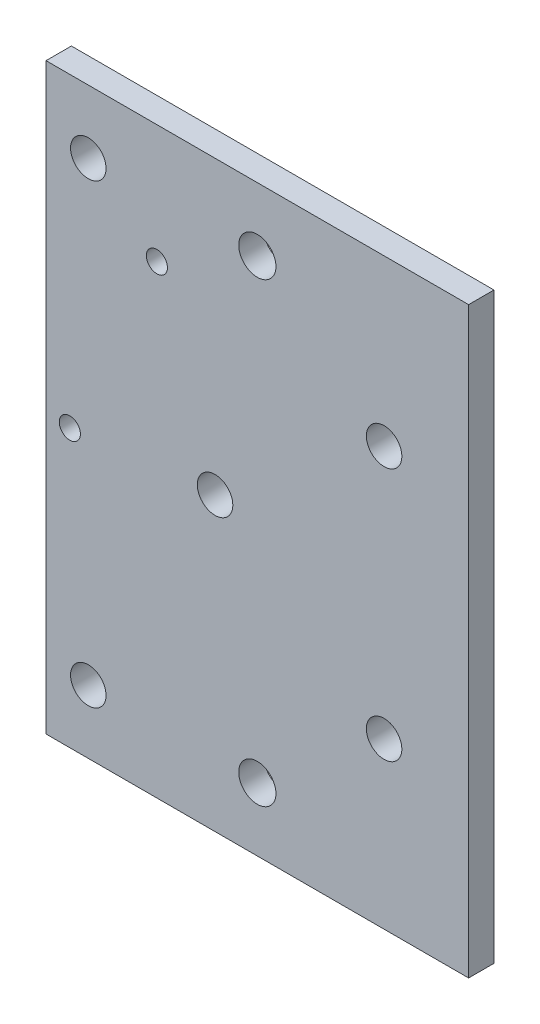
SolidWorks part; units mm, degrees
ref_plane "正面" through (0, 0, 0) normal (0, 0, 1) x (1, 0, 0)
ref_plane "平面" through (0, 0, 0) normal (0, 1, 0) x (1, 0, 0)
ref_plane "右側面" through (0, 0, 0) normal (1, 0, 0) x (0, 0, -1)
sketch "ｽｹｯﾁ1" plane through (0, 0, 0) normal (0, 0, 1) x (1, 0, 0)
  line L1 (-20, 14.5) -> (20, 14.5)
  line L2 (-20, 14.5) -> (-20, -14.5)
  line L3 (-20, -14.5) -> (20, -14.5)
  line L4 (20, 14.5) -> (20, -14.5)
  line L5 (-20, 14.5) -> (20, -14.5) construction
  line L6 (-20, -14.5) -> (20, 14.5) construction
  point P0 (0, 0)
  dimension "D1" = 29
  dimension "D2" = 40
extrude "ﾎﾞｽ - 押し出し1" add sketch "ｽｹｯﾁ1" along normal blind 3
sketch "ｽｹｯﾁ2" plane through (0, 0, 3) normal (0, 0, 1) x (1, 0, 0)
  line L1 (-20, 14.5) -> (-16.5, 14.5)
  line L2 (-20, 14.5) -> (-20, 10.5)
  line L3 (-20, 10.5) -> (-16.5, 10.5)
  line L4 (-16.5, 14.5) -> (-16.5, 10.5)
  line L5 (-20, -14.5) -> (-16.5, -14.5)
  line L6 (-20, -14.5) -> (-20, -10.5)
  line L7 (-20, -10.5) -> (-16.5, -10.5)
  line L8 (-16.5, -14.5) -> (-16.5, -10.5)
  line L9 (20, -14.5) -> (16.5, -14.5)
  line L10 (20, -14.5) -> (20, -10.5)
  line L11 (20, -10.5) -> (16.5, -10.5)
  line L12 (16.5, -14.5) -> (16.5, -10.5)
  line L13 (20, 14.5) -> (16.5, 14.5)
  line L14 (20, 14.5) -> (20, 10.5)
  line L15 (20, 10.5) -> (16.5, 10.5)
  line L16 (16.5, 14.5) -> (16.5, 10.5)
  circle A0 centre (-16.5, 10.5) radius 2.1
  circle A1 centre (-16.5, -10.5) radius 2.1
  circle A2 centre (16.5, -10.5) radius 2.1
  circle A3 centre (16.5, 10.5) radius 2.1
  dimension "D9" = 4.2
  dimension "D10" = 4.2
  dimension "D11" = 4.2
  dimension "D12" = 4.2
  dimension "D1" = 3.5
  dimension "D2" = 4
  dimension "D3" = 3.5
  dimension "D4" = 4
  dimension "D5" = 3.5
  dimension "D6" = 4
  dimension "D7" = 3.5
  dimension "D8" = 4
sketch "ｽｹｯﾁ3" plane through (0, -14.5, 0) normal (0, -1, 0) x (-1, 0, 0)
  line L0 (20, 0) -> (-20, 0) construction
  line L1 (20, -3) -> (-20, -3)
  line L2 (20, -3) -> (20, 0)
  line L3 (20, 0) -> (-20, 0)
  line L4 (-20, -3) -> (-20, 0)
extrude "ﾎﾞｽ - 押し出し2" add sketch "ｽｹｯﾁ3" along normal blind 3
sketch "ｽｹｯﾁ4" plane through (0, 14.5, 0) normal (0, 1, 0) x (1, 0, 0)
  line L1 (20, -3) -> (-20, -3)
  line L2 (20, -3) -> (20, 0)
  line L3 (20, 0) -> (-20, 0)
  line L4 (-20, -3) -> (-20, 0)
extrude "ﾎﾞｽ - 押し出し3" add sketch "ｽｹｯﾁ4" along normal blind 3
sketch "ｽｹｯﾁ5" plane through (0, -17.5, 0) normal (0, -1, 0) x (1, 0, 0)
  line L1 (20, 3) -> (-20, 3)
  line L2 (20, 3) -> (20, 0)
  line L3 (20, 0) -> (-20, 0)
  line L4 (-20, 3) -> (-20, 0)
extrude "ﾎﾞｽ - 押し出し4" add sketch "ｽｹｯﾁ5" along normal blind 7
sketch "ｽｹｯﾁ6" plane through (0, 17.5, 0) normal (0, 1, 0) x (1, 0, 0)
  line L1 (-20, -3) -> (20, -3)
  line L2 (-20, -3) -> (-20, 0)
  line L3 (-20, 0) -> (20, 0)
  line L4 (20, -3) -> (20, 0)
extrude "ﾎﾞｽ - 押し出し5" add sketch "ｽｹｯﾁ6" along normal blind 7
sketch "ｽｹｯﾁ7" plane through (0, 24.5, 0) normal (0, 1, 0) x (1, 0, 0)
  line L1 (-20, -3) -> (20, -3)
  line L2 (-20, -3) -> (-20, 0)
  line L3 (-20, 0) -> (20, 0)
  line L4 (20, -3) -> (20, 0)
extrude "ﾎﾞｽ - 押し出し6" add sketch "ｽｹｯﾁ7" along normal blind 10
sketch "ｽｹｯﾁ8" plane through (0, -24.5, 0) normal (0, -1, 0) x (1, 0, 0)
  line L1 (20, 3) -> (-20, 3)
  line L2 (20, 3) -> (20, 0)
  line L3 (20, 0) -> (-20, 0)
  line L4 (-20, 3) -> (-20, 0)
extrude "ﾎﾞｽ - 押し出し7" add sketch "ｽｹｯﾁ8" along normal blind 10
sketch "ｽｹｯﾁ9" plane through (0, 0, 3) normal (0, 0, 1) x (1, 0, 0)
  line L0 (20, 34.5) -> (20, 27)
  line L1 (20, -34.5) -> (20, 34.5) construction
  line L2 (20, 27) -> (-5, 27)
  line L3 (-20, 34.5) -> (-20, 27)
  line L4 (-20, 34.5) -> (-20, -34.5) construction
  line L5 (-20, 27) -> (-25, 27)
  circle A0 centre (-5, 27) radius 2.2
  circle A1 centre (-25, 27) radius 2.2
  dimension "D5" = 4.4
  dimension "D6" = 4.4
  dimension "D1" = 7.5
  dimension "D2" = 25
  dimension "D3" = 7.5
  dimension "D4" = 5
extrude "ｶｯﾄ - 押し出し2" cut sketch "ｽｹｯﾁ9" against normal blind 15
sketch "ｽｹｯﾁ10" plane through (0, 0, 3) normal (0, 0, 1) x (1, 0, 0)
  line L0 (20, -34.5) -> (20, -27)
  line L1 (20, -34.5) -> (20, 34.5) construction
  line L2 (20, -27) -> (-5, -27)
  line L3 (20, -27) -> (-15, -27)
  circle A0 centre (-5, -27) radius 2.2
  circle A1 centre (-15, -27) radius 2.2
  dimension "D4" = 4.4
  dimension "D5" = 4.4
  dimension "D1" = 7.5
  dimension "D2" = 25
  dimension "D3" = 35
extrude "ｶｯﾄ - 押し出し3" cut sketch "ｽｹｯﾁ10" against normal through all contours L3 A0 | L3 A0
sketch "ｽｹｯﾁ11" plane through (20, 0, 0) normal (1, 0, 0) x (0, 0, -1)
  line L1 (0, 34.5) -> (-3, 34.5)
  line L2 (0, 34.5) -> (0, -34.5)
  line L3 (0, -34.5) -> (-3, -34.5)
  line L4 (-3, 34.5) -> (-3, -34.5)
  line L5 (-3, 34.5) -> (0, 34.5)
  line L6 (-3, 34.5) -> (-3, -34.5)
  line L7 (-3, -34.5) -> (0, -34.5)
  line L8 (0, 34.5) -> (0, -34.5)
sketch "ｽｹｯﾁ12" plane through (-20, 0, 0) normal (-1, 0, 0) x (0, 0, 1)
  line L1 (3, 34.5) -> (0, 34.5)
  line L2 (3, 34.5) -> (3, -34.5)
  line L3 (3, -34.5) -> (0, -34.5)
  line L4 (0, 34.5) -> (0, -34.5)
extrude "ﾎﾞｽ - 押し出し9" add sketch "ｽｹｯﾁ12" along normal blind 30
sketch "ｽｹｯﾁ15" plane through (0, 0, 3) normal (0, 0, 1) x (1, 0, 0)
  line L0 (-50, 0) -> (-10, 0)
  line L1 (-50, -34.5) -> (-50, 34.5) construction
  circle A0 centre (-10, 0) radius 2.1
  dimension "D2" = 4.2
  dimension "D1" = 40
extrude "ｶｯﾄ - 押し出し4" cut sketch "ｽｹｯﾁ15" against normal blind 10
sketch "ｽｹｯﾁ16" plane through (0, 0, 0) normal (0, 0, -1) x (-1, 0, 0)
  line L0 (-20, 0) -> (-10, 0)
  line L2 (-20, -34.5) -> (-20, 34.5) construction
  line L3 (-10, 0) -> (-10, -15)
  line L5 (-10, 0) -> (-10, 15)
  circle A0 centre (-10, -15) radius 2.1
  circle A1 centre (-10, 15) radius 2.1
  dimension "D3" = 4.2
  dimension "D4" = 4.2
  dimension "D1" = 15
  dimension "D2" = 15
  dimension "D5" = 10
extrude "ｶｯﾄ - 押し出し5" cut sketch "ｽｹｯﾁ16" against normal blind 10
sketch "ｽｹｯﾁ17" plane through (-50, 0, 0) normal (-1, 0, 0) x (0, 0, 1)
  line L1 (3, -34.5) -> (0, -34.5)
  line L2 (3, -34.5) -> (3, 34.5)
  line L3 (3, 34.5) -> (0, 34.5)
  line L4 (0, -34.5) -> (0, 34.5)
extrude "ｶｯﾄ - 押し出し6" cut sketch "ｽｹｯﾁ17" against normal blind 20
sketch "ｽｹｯﾁ18" plane through (0, 0, 3) normal (0, 0, 1) x (1, 0, 0)
  line L1 (-16.8819, 20.4634) -> (-30, 20.4634)
  line L2 (-30, -34.5) -> (-30, 34.5) construction
  line L3 (-30, 20.4634) -> (-30, 34.5)
  line L5 (-27.1819, -1.7366) -> (-16.8819, -1.7366)
  line L6 (-16.8819, -1.7366) -> (-16.8819, 20.4634)
  circle A0 centre (-16.8819, 20.4634) radius 2.5705
  circle A1 centre (-27.1819, -1.7366) radius 2.8
  dimension "D1" = 22.2
  dimension "D2" = 10.3
hole_wizard "M3x0.5 ねじ穴1" positions "3Dｽｹｯﾁ1" profile "ｽｹｯﾁ19" tap size "M3x0.5" standard "JIS"
sketch3d "3Dｽｹｯﾁ1"
  point P0 (-16.8819, 20.4634, 3)
  point P3 (-27.1819, -1.7366, 3)
sketch "ｽｹｯﾁ19" plane through (-16.8819, 20.4634, 3) normal (1, 0, 0) x (0, -1, 0)
  line L0 (0, 0) -> (0, 9.2511)
  line L1 (0, 9.2511) -> (1.25, 8.5)
  line L2 (1.25, 8.5) -> (1.25, 0)
  line L5 (1.25, 0) -> (0, 0)
  line L10 (0, 9.2511) -> (-1.25, 8.5) construction
  line L11 (0, -6.35) -> (0, 107.95) construction
  dimension "ねじ下穴ﾄﾞﾘﾙ直径" = 2.5
  dimension "ねじ下穴ﾄﾞﾘﾙの深さ" = 8.5
  dimension "ﾄﾞﾘﾙ角度" = 118
cosmetic thread "穴のねじ山1" parameters "D1"=3, "D2"=3
cosmetic thread "穴のねじ山2" parameters "D1"=3, "D2"=3
sketch "ｽｹｯﾁ20" plane through (0, 0, 0) normal (0, 0, -1) x (-1, 0, 0)
  line L0 (30, -34.5) -> (30, -27)
  line L1 (30, 34.5) -> (30, -34.5) construction
  line L2 (30, -27) -> (25, -27)
  line L3 (30, 34.5) -> (30, 27)
  line L4 (30, 20.4634) -> (30, 34.5) construction
  line L5 (30, 27) -> (25, 27)
  circle A0 centre (25, -27) radius 2.1
  circle A1 centre (25, 27) radius 2.1
  dimension "D3" = 4.2
  dimension "D6" = 4.2
  dimension "D1" = 7.5
  dimension "D2" = 5
  dimension "D4" = 7.5
  dimension "D5" = 5
extrude "ｶｯﾄ - 押し出し7" cut sketch "ｽｹｯﾁ20" against normal blind 10
